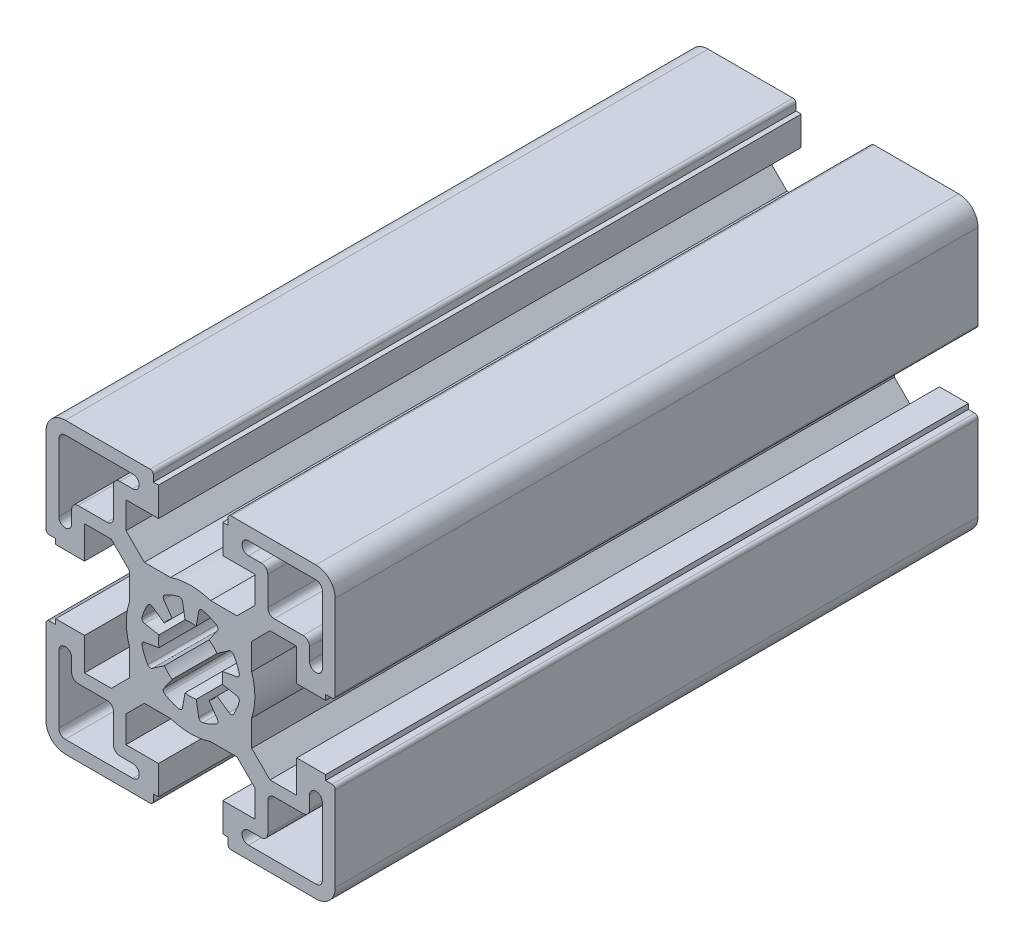
SolidWorks part; units mm, degrees
ref_plane "Front Plane" through (0, 0, 0) normal (0, 0, 1) x (1, 0, 0)
ref_plane "Top Plane" through (0, 0, 0) normal (0, 1, 0) x (1, 0, 0)
ref_plane "Right Plane" through (0, 0, 0) normal (1, 0, 0) x (0, 0, -1)
sketch "Sketch1" plane through (0, 0, 0) normal (0, 0, 1) x (1, 0, 0)
  line L0 (0, 34.901) -> (0, -38.8683) construction
  line L1 (-27.7848, 0) -> (42.6814, 0) construction
  line L3 (2.8679, -4.0957) -> (4.1737, -5.9606)
  line L4 (-4.1737, -5.9606) -> (-2.8679, -4.0957)
  line L5 (-0.8682, -4.924) -> (-1.2635, -7.166)
  line L6 (0.8682, -4.924) -> (1.2636, -7.166)
  line L7 (4.0957, -2.8679) -> (5.9606, -4.1736)
  line L8 (4.924, -0.8682) -> (7.166, -1.2636)
  line L9 (-7.166, -1.2636) -> (-4.924, -0.8682)
  line L10 (-4.0957, -2.8679) -> (-5.9606, -4.1736)
  line L88 (0.8682, 4.924) -> (1.2636, 7.166)
  line L89 (-0.8682, 4.924) -> (-1.2635, 7.166)
  line L90 (-4.1737, 5.9606) -> (-2.8679, 4.0957)
  line L91 (-4.0957, 2.8679) -> (-5.9606, 4.1736)
  line L92 (-7.166, 1.2636) -> (-4.924, 0.8682)
  line L101 (4.924, 0.8682) -> (7.166, 1.2636)
  line L102 (4.0957, 2.8679) -> (5.9606, 4.1736)
  line L103 (2.8679, 4.0957) -> (4.1737, 5.9606)
  line L104 (-5, -16.4999) -> (-5, -20.9999)
  line L105 (-5, -20.9999) -> (-5.8, -20.9999)
  line L106 (-5.8, -20.9999) -> (-5.8, -22)
  line L107 (-6.3, -22.5) -> (-19.5, -22.5)
  line L108 (-22.5, -19.5) -> (-22.5, -6.2999)
  line L109 (-22, -5.7999) -> (-21, -5.7999)
  line L110 (-21, -5.7999) -> (-21, -4.9999)
  line L111 (-21, -4.9999) -> (-16.5, -4.9999)
  line L112 (-16.5, -4.9999) -> (-16.5, -10.0499)
  line L113 (-16.5, -10.0499) -> (-12.3429, -10.0499)
  line L114 (-12.3429, -10.0499) -> (-9.5, -7.207)
  line L115 (-9.5, -7.207) -> (-9.5, -3.1226)
  line L116 (-9.5, 3.1227) -> (-9.5, 7.207)
  line L117 (-9.5, 7.207) -> (-12.3429, 10.0499)
  line L118 (-12.3429, 10.0499) -> (-16.5, 10.0499)
  line L119 (-16.5, 10.0499) -> (-16.5, 4.9999)
  line L120 (-16.5, 4.9999) -> (-21, 4.9999)
  line L121 (-21, 4.9999) -> (-21, 5.7999)
  line L122 (-21, 5.7999) -> (-22, 5.7999)
  line L123 (-22.5, 6.2999) -> (-22.5, 19.5)
  line L124 (-19.5, 22.5) -> (-6.3, 22.5)
  line L125 (-5.7999, 21.9999) -> (-5.7999, 20.9999)
  line L126 (-5.7999, 20.9999) -> (-5, 20.9999)
  line L127 (-5, 20.9999) -> (-5, 16.5)
  line L128 (-5, 16.5) -> (-10.0501, 16.5)
  line L129 (-10.0501, 16.5) -> (-10.0501, 12.3428)
  line L130 (-10.0501, 12.3428) -> (-7.2072, 9.4999)
  line L131 (-7.2072, 9.4999) -> (-3.1228, 9.4999)
  line L132 (3.1226, 9.4999) -> (7.207, 9.4999)
  line L133 (7.207, 9.4999) -> (10.0499, 12.3428)
  line L134 (10.0499, 12.3428) -> (10.0499, 16.5)
  line L135 (10.0499, 16.5) -> (5, 16.5)
  line L136 (5, 16.5) -> (5, 21)
  line L137 (5, 21) -> (5.7999, 21)
  line L138 (5.7999, 21) -> (5.7999, 21.9999)
  line L139 (6.3, 22.5) -> (19.5001, 22.5)
  line L140 (22.5001, 6.2999) -> (22.5001, 19.5)
  line L141 (22.0001, 5.7999) -> (21, 5.7999)
  line L142 (21, 5.7999) -> (21, 4.9999)
  line L143 (21, 4.9999) -> (16.5, 4.9999)
  line L144 (16.5, 4.9999) -> (16.5, 10.0499)
  line L145 (16.5, 10.0499) -> (12.3429, 10.0499)
  line L146 (12.3429, 10.0499) -> (9.4999, 7.207)
  line L147 (9.4999, 7.207) -> (9.4999, 3.1227)
  line L148 (9.4999, -3.1226) -> (9.4999, -7.207)
  line L149 (9.4999, -7.207) -> (12.3429, -10.0499)
  line L150 (12.3429, -10.0499) -> (16.5, -10.0499)
  line L151 (16.5, -10.0499) -> (16.5, -4.9999)
  line L152 (16.5, -4.9999) -> (21, -4.9999)
  line L153 (21, -4.9999) -> (21, -5.7999)
  line L154 (21, -5.7999) -> (22.0001, -5.7999)
  line L155 (22.5001, -6.2999) -> (22.5001, -19.5)
  line L156 (6.3, -22.5) -> (19.5001, -22.5)
  line L157 (5.8, -22) -> (5.8, -20.9999)
  line L158 (5.8, -20.9999) -> (5, -20.9999)
  line L159 (5, -20.9999) -> (5, -16.4999)
  line L160 (5, -16.4999) -> (10.0499, -16.4999)
  line L161 (10.0499, -16.4999) -> (10.0499, -12.3428)
  line L162 (10.0499, -12.3428) -> (7.2069, -9.4998)
  line L163 (7.2069, -9.4998) -> (3.1226, -9.4998)
  line L164 (-3.1228, -9.4998) -> (-7.2071, -9.4998)
  line L165 (-7.2071, -9.4998) -> (-10.0501, -12.3428)
  line L166 (-10.0501, -12.3428) -> (-10.0501, -16.4999)
  line L167 (-10.0501, -16.4999) -> (-5, -16.4999)
  line L168 (-17.5001, -12) -> (-13.0001, -12)
  line L169 (-12.0001, -17.4999) -> (-12.0001, -13)
  line L170 (-11.0001, -18.4999) -> (-9.0001, -18.4999)
  line L171 (-19.5001, -20.5) -> (-9.0001, -20.5)
  line L172 (-20.5001, -19.5) -> (-20.5001, -8.9999)
  line L173 (-18.5001, -11) -> (-18.5001, -8.9999)
  line L174 (13, -12) -> (17.5, -12)
  line L175 (12, -17.4999) -> (12, -13)
  line L176 (9, -18.4999) -> (11, -18.4999)
  line L177 (9, -20.5) -> (19.5, -20.5)
  line L178 (20.5, -19.5) -> (20.5, -9.0001)
  line L179 (18.5, -11) -> (18.5, -9.0001)
  line L180 (-17.5001, 12) -> (-13.0001, 12)
  line L181 (-12.0001, 13) -> (-12.0001, 17.4999)
  line L182 (-11.0001, 18.4999) -> (-9.0001, 18.4999)
  line L183 (-19.5001, 20.5) -> (-9.0001, 20.5)
  line L184 (-20.5001, 8.9999) -> (-20.5001, 19.5)
  line L185 (-18.5001, 8.9999) -> (-18.5001, 11)
  line L186 (13, 12) -> (17.5, 12)
  line L187 (12, 13) -> (12, 17.4999)
  line L188 (9, 18.4999) -> (11, 18.4999)
  line L189 (9, 20.5) -> (19.5, 20.5)
  line L190 (20.5, 9.0001) -> (20.5, 19.5)
  line L191 (18.5, 9.0001) -> (18.5, 11)
  arc A0 (4.0221, -6.6756) -> (1.8763, -7.5644) centre (0, 0) cw
  arc A1 (-1.8763, -7.5645) -> (-4.0221, -6.6756) centre (0, 0) cw
  arc A2 (7.5644, -1.8763) -> (7.166, -1.2636) centre (7.0792, -1.756) ccw
  arc A3 (6.6756, -4.0221) -> (5.9606, -4.1736) centre (6.2474, -3.7641) cw
  arc A4 (4.0221, -6.6756) -> (4.1737, -5.9606) centre (3.7641, -6.2474) ccw
  arc A5 (1.8763, -7.5644) -> (1.2636, -7.166) centre (1.756, -7.0792) cw
  arc A6 (4.0957, -2.8679) -> (2.8679, -4.0957) centre (0, 0) cw
  arc A7 (7.5644, -1.8763) -> (6.6756, -4.0221) centre (0, 0) cw
  arc A8 (-1.8763, -7.5645) -> (-1.2635, -7.166) centre (-1.7559, -7.0792) ccw
  arc A9 (-4.0221, -6.6756) -> (-4.1737, -5.9606) centre (-3.7641, -6.2474) cw
  arc A10 (-6.6756, -4.0221) -> (-5.9606, -4.1736) centre (-6.2474, -3.7641) ccw
  arc A11 (-7.5644, -1.8763) -> (-7.166, -1.2636) centre (-7.0792, -1.756) cw
  arc A12 (7.166, 1.2636) -> (7.5644, 1.8763) centre (7.0792, 1.756) ccw
  arc A13 (6.6756, 4.0221) -> (5.9606, 4.1736) centre (6.2474, 3.7641) ccw
  arc A14 (4.1737, 5.9606) -> (4.0221, 6.6756) centre (3.7641, 6.2474) ccw
  arc A15 (1.8763, 7.5644) -> (1.2636, 7.166) centre (1.756, 7.0792) ccw
  arc A16 (-6.6756, -4.0221) -> (-7.5644, -1.8763) centre (0, 0) cw
  arc A17 (-2.8679, -4.0957) -> (-4.0957, -2.8679) centre (0, 0) cw
  arc A18 (0.8682, -4.924) -> (-0.8682, -4.924) centre (0, 0) cw
  arc A19 (-1.2635, 7.166) -> (-1.8763, 7.5645) centre (-1.7559, 7.0792) ccw
  arc A20 (-4.0221, 6.6756) -> (-4.1737, 5.9606) centre (-3.7641, 6.2474) ccw
  arc A21 (-7.166, 1.2636) -> (-7.5644, 1.8763) centre (-7.0792, 1.756) cw
  arc A22 (-6.6756, 4.0221) -> (-5.9606, 4.1736) centre (-6.2474, 3.7641) cw
  arc A56 (0.8682, 4.924) -> (-0.8682, 4.924) centre (0, 0) ccw
  arc A57 (-1.8763, 7.5645) -> (-4.0221, 6.6756) centre (0, 0) ccw
  arc A58 (-2.8679, 4.0957) -> (-4.0957, 2.8679) centre (0, 0) ccw
  arc A59 (-6.6756, 4.0221) -> (-7.5644, 1.8763) centre (0, 0) ccw
  arc A60 (-4.924, 0.8682) -> (-4.924, -0.8682) centre (0, 0) ccw
  arc A68 (4.924, -0.8682) -> (4.924, 0.8682) centre (0, 0) ccw
  arc A69 (7.5644, 1.8763) -> (6.6756, 4.0221) centre (0, 0) ccw
  arc A70 (4.0957, 2.8679) -> (2.8679, 4.0957) centre (0, 0) ccw
  arc A71 (4.0221, 6.6756) -> (1.8763, 7.5644) centre (0, 0) ccw
  arc A72 (-6.3, -22.5) -> (-5.8, -22) centre (-6.3, -22) ccw
  arc A73 (-22.5, -19.5) -> (-19.5, -22.5) centre (-19.5, -19.5) ccw
  arc A74 (-22, -5.7999) -> (-22.5, -6.2999) centre (-22, -6.2999) ccw
  arc A75 (-9.5, 3.1227) -> (-9.5, -3.1226) centre (0, 0.0001) ccw
  arc A76 (-22.5, 6.2999) -> (-22, 5.7999) centre (-22, 6.2999) ccw
  arc A77 (-19.5, 22.5) -> (-22.5, 19.5) centre (-19.5, 19.5) ccw
  arc A78 (-5.7999, 21.9999) -> (-6.3, 22.5) centre (-6.3, 21.9999) ccw
  arc A79 (3.1226, 9.4999) -> (-3.1228, 9.4999) centre (-0.0001, -0.0001) ccw
  arc A80 (6.3, 22.5) -> (5.7999, 21.9999) centre (6.3, 21.9999) ccw
  arc A81 (22.5001, 19.5) -> (19.5001, 22.5) centre (19.5001, 19.5) ccw
  arc A82 (22.0001, 5.7999) -> (22.5001, 6.2999) centre (22.0001, 6.2999) ccw
  arc A83 (9.4999, -3.1226) -> (9.4999, 3.1227) centre (0, 0.0001) ccw
  arc A84 (22.5001, -6.2999) -> (22.0001, -5.7999) centre (22.0001, -6.2999) ccw
  arc A85 (19.5001, -22.5) -> (22.5001, -19.5) centre (19.5001, -19.5) ccw
  arc A86 (5.8, -22) -> (6.3, -22.5) centre (6.3, -22) ccw
  arc A87 (-3.1228, -9.4998) -> (3.1226, -9.4998) centre (-0.0001, 0.0001) ccw
  arc A88 (-18.5001, -11) -> (-17.5001, -12) centre (-17.5001, -11) ccw
  arc A89 (-12.0001, -13) -> (-13.0001, -12) centre (-13.0001, -13) ccw
  arc A90 (-12.0001, -17.4999) -> (-11.0001, -18.4999) centre (-11.0001, -17.4999) ccw
  arc A91 (-9.0001, -20.5) -> (-9.0001, -18.4999) centre (-9.0001, -19.5) ccw
  arc A92 (-20.5001, -19.5) -> (-19.5001, -20.5) centre (-19.5001, -19.5) ccw
  arc A93 (-18.5001, -8.9999) -> (-20.5001, -8.9999) centre (-19.5001, -8.9999) ccw
  arc A94 (17.5, -12) -> (18.5, -11) centre (17.5, -11) ccw
  arc A95 (13, -12) -> (12, -13) centre (13, -13) ccw
  arc A96 (11, -18.4999) -> (12, -17.4999) centre (11, -17.4999) ccw
  arc A97 (9, -18.4999) -> (9, -20.5) centre (9, -19.5) ccw
  arc A98 (19.5, -20.5) -> (20.5, -19.5) centre (19.5, -19.5) ccw
  arc A99 (20.5, -9.0001) -> (18.5, -9.0001) centre (19.5, -9.0001) ccw
  arc A100 (-17.5001, 12) -> (-18.5001, 11) centre (-17.5001, 11) ccw
  arc A101 (-13.0001, 12) -> (-12.0001, 13) centre (-13.0001, 13) ccw
  arc A102 (-11.0001, 18.4999) -> (-12.0001, 17.4999) centre (-11.0001, 17.4999) ccw
  arc A103 (-9.0001, 18.4999) -> (-9.0001, 20.5) centre (-9.0001, 19.5) ccw
  arc A104 (-19.5001, 20.5) -> (-20.5001, 19.5) centre (-19.5001, 19.5) ccw
  arc A105 (-20.5001, 8.9999) -> (-18.5001, 8.9999) centre (-19.5001, 8.9999) ccw
  arc A106 (18.5, 11) -> (17.5, 12) centre (17.5, 11) ccw
  arc A107 (12, 13) -> (13, 12) centre (13, 13) ccw
  arc A108 (12, 17.4999) -> (11, 18.4999) centre (11, 17.4999) ccw
  arc A109 (9, 20.5) -> (9, 18.4999) centre (9, 19.5) ccw
  arc A110 (20.5, 19.5) -> (19.5, 20.5) centre (19.5, 19.5) ccw
  arc A111 (18.5, 9.0001) -> (20.5, 9.0001) centre (19.5, 9.0001) ccw
  dimension "D5" = 10
  dimension "D7" = 0.5
  dimension "D1" = 45.0001
  dimension "D2" = 44.9999
  dimension "D3" = 12.5001
  dimension "D4" = 10
  dimension "D6" = 22.5001
extrude "Base-Extrude" add sketch "Sketch1" along normal blind 100
